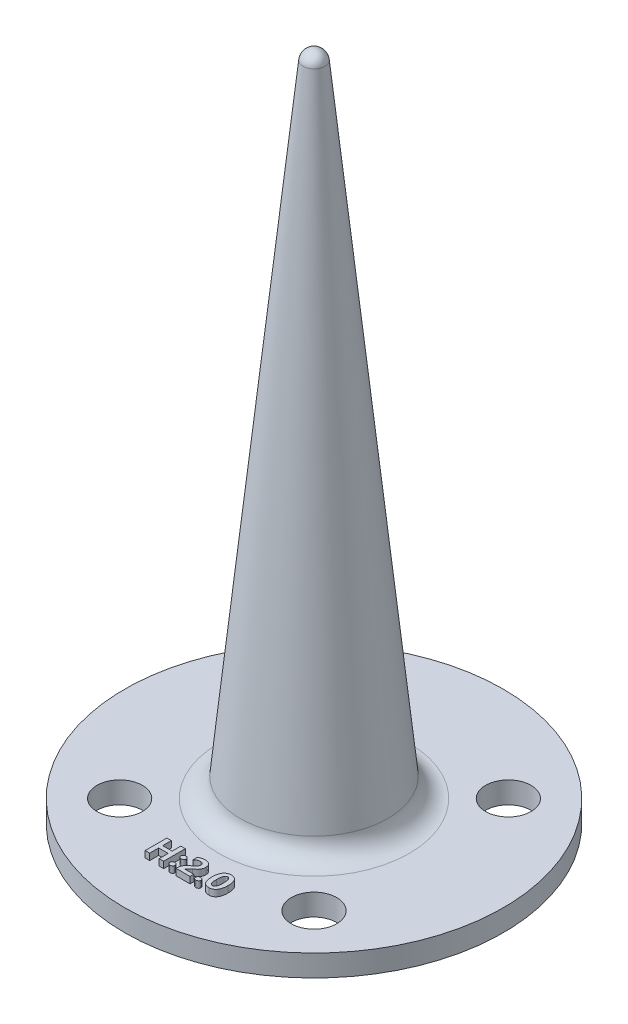
SolidWorks part; units mm, degrees
ref_plane "前视基准面" through (0, 0, 0) normal (0, 0, 1) x (1, 0, 0)
ref_plane "上视基准面" through (0, 0, 0) normal (0, 1, 0) x (1, 0, 0)
ref_plane "右视基准面" through (0, 0, 0) normal (1, 0, 0) x (0, 0, -1)
sketch "草图1" plane through (0, 0, 0) normal (0, 1, 0) x (1, 0, 0)
  circle A0 centre (0, 0) radius 17.5
  dimension "D1" = 35
extrude "凸台-拉伸1" add sketch "草图1" along normal blind 2
sketch "草图2" plane through (0, 2, 0) normal (0, 1, 0) x (1, 0, 0)
  line L0 (0, 0) -> (0, 3.7839) construction
  line L1 (0, 0) -> (3.1047, 0) construction
  line L2 (0, 0) -> (-6.2166, 6.2166) construction
  line L3 (0, 0) -> (4.9724, 4.9724) construction
  circle A2 centre (0, 0) radius 12.7 construction
  circle A3 centre (-8.9803, 8.9803) radius 2.1
  circle A4 centre (8.9803, 8.9803) radius 2.1
  circle A5 centre (8.9803, -8.9803) radius 2.1
  circle A6 centre (-8.9803, -8.9803) radius 2.1
  point P20 (0, 0)
  dimension "D1" = 45
  dimension "D2" = 25.4
  dimension "D3" = 4.2
extrude "切除-拉伸1" cut sketch "草图2" against normal through all
sketch "草图3" plane through (0, 0, 0) normal (0, 0, 1) x (1, 0, 0)
  line L0 (0, 2) -> (0, 62)
  line L1 (17.5, 2) -> (-17.5, 2) construction
  line L2 (-0.1119, 62) -> (1.772, 62) construction
  line L4 (8.5, 2) -> (8.5, 0) construction
  line L5 (-17.5, 0) -> (17.5, 0) construction
  line L6 (8.5, 0) -> (3.5, 0)
  line L7 (3, -0.5) -> (3, -1.5)
  line L8 (2.5, -2) -> (0, -2)
  line L9 (0, 2) -> (0, -2)
  line L10 (3, -0.5) -> (3, 0)
  line L11 (1, 61.0964) -> (6.8175, 3.798)
  line L12 (8.8072, 2) -> (8.5, 2)
  line L13 (8.5, 2) -> (8.5, 0)
  line L14 (3, 0) -> (3.5, 0)
  arc A0 (0, 62) -> (1, 61.0964) centre (0, 60.9949) cw
  arc A1 (8.8072, 2) -> (6.8175, 3.798) centre (8.8072, 4) cw
  arc A3 (3, -1.5) -> (2.5, -2) centre (2.5, -1.5) cw
  point P19 (7, 2)
  point P22 (3, 0)
  point P25 (3, -2)
  dimension "D7" = 2
  dimension "D1" = 3
  dimension "D2" = 60
  dimension "D3" = 8.5
  dimension "D4" = 2
  dimension "D5" = 1
  dimension "D6" = 7
revolve "旋转1" add sketch "草图3" angle 360 about L0
sketch "草图4" plane through (0, 2, 0) normal (0, 1, 0) x (1, 0, 0)
  text T0 "<b>H:2.0</b>" font "微软雅黑" height 2
extrude "凸台-拉伸2" add sketch "草图4" along normal blind 0.6
